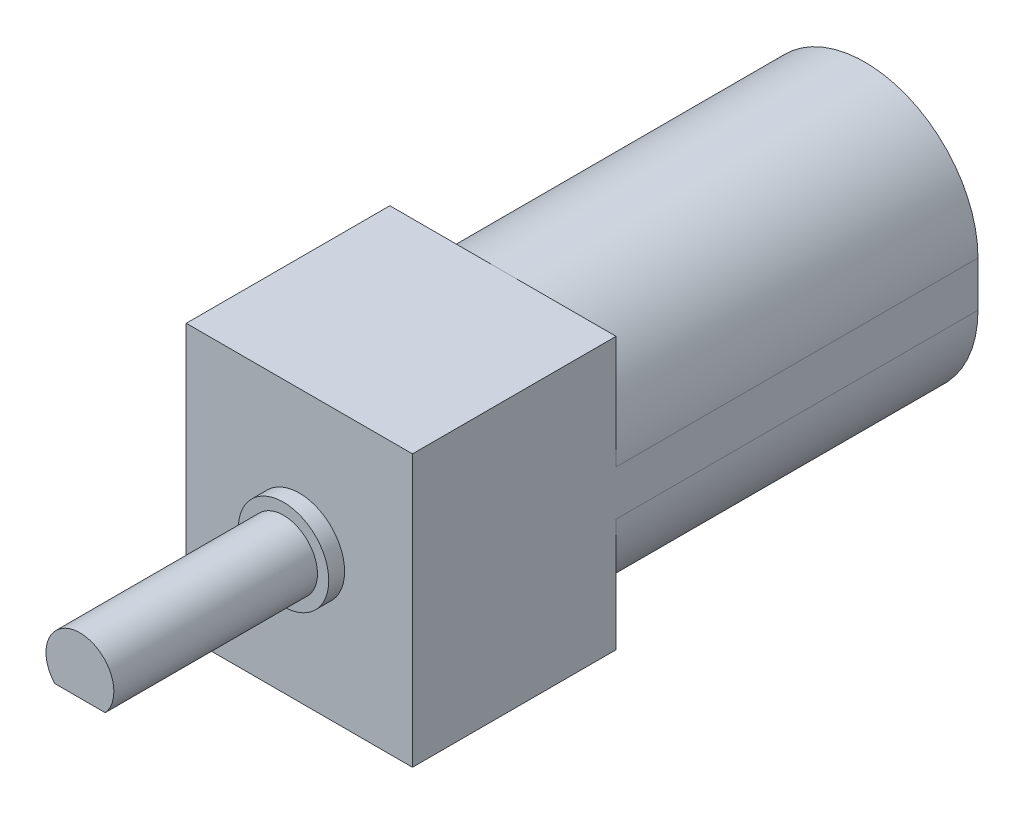
SolidWorks part; units mm, degrees
ref_plane "Ebene vorne" through (0, 0, 0) normal (0, 0, 1) x (1, 0, 0)
ref_plane "Ebene oben" through (0, 0, 0) normal (0, 1, 0) x (1, 0, 0)
ref_plane "Ebene rechts" through (0, 0, 0) normal (1, 0, 0) x (0, 0, -1)
sketch "Sketch1" plane through (0, 0, 0) normal (0, 0, 1) x (1, 0, 0)
  line L0 (0, -1) -> (0, 1) construction
  line L1 (-5, -1) -> (-5, 1)
  line L2 (5, -1) -> (5, 1)
  arc A0 (-5, -1) -> (5, -1) centre (0, -1) ccw
  arc A1 (5, 1) -> (-5, 1) centre (0, 1) ccw
  point P3 (0, 0)
  dimension "D2" = 12
  dimension "D1" = 10
extrude "Boss-Extrude1" add sketch "Sketch1" along normal blind 16
sketch "Sketch2" plane through (0, 0, 0) normal (0, 0, -1) x (-1, 0, 0)
  circle A0 centre (0, 0) radius 2.5
  dimension "D1" = 5
extrude "Boss-Extrude2" add sketch "Sketch2" along normal blind 1.3
sketch "Sketch3" plane through (0, 0, 16) normal (0, 0, 1) x (1, 0, 0)
  line L0 (-5, 1) -> (-5, -1) construction
  line L1 (5, -6) -> (-5, -6)
  line L2 (5, -6) -> (5, 6)
  line L3 (5, 6) -> (-5, 6)
  line L4 (-5, -6) -> (-5, 6)
  line L5 (5, -6) -> (-5, 6) construction
  line L6 (5, 6) -> (-5, -6) construction
  point P0 (0, 0)
  dimension "D1" = 12
extrude "Boss-Extrude3" add sketch "Sketch3" along normal blind 9
sketch "Sketch4" plane through (0, 0, 25) normal (0, 0, 1) x (1, 0, 0)
  circle A0 centre (0, 0) radius 2
  dimension "D1" = 4
extrude "Boss-Extrude4" add sketch "Sketch4" along normal blind 0.7
sketch "Sketch5" plane through (0, 0, 25.7) normal (0, 0, 1) x (1, 0, 0)
  circle A0 centre (0, 0) radius 1.5
  dimension "D1" = 3
extrude "Boss-Extrude5" add sketch "Sketch5" along normal blind 9
sketch "Sketch6" plane through (0, 0, 34.7) normal (0, 0, 1) x (1, 0, 0)
  line L1 (2.6743, -1) -> (-2.6743, -1)
  line L2 (2.6743, -1) -> (2.6743, -2.4157)
  line L3 (2.6743, -2.4157) -> (-2.6743, -2.4157)
  line L4 (-2.6743, -1) -> (-2.6743, -2.4157)
  line L5 (2.6743, -1) -> (-2.6743, -2.4157) construction
  line L6 (2.6743, -2.4157) -> (-2.6743, -1) construction
  circle A4 centre (0, 0) radius 1.5 construction
  point P0 (0, -1.7078)
  dimension "D1" = 2.5
  dimension "D2" = 1.4157
  dimension "D3" = 5.3485
extrude "Cut-Extrude1" cut sketch "Sketch6" against normal blind 8.9
